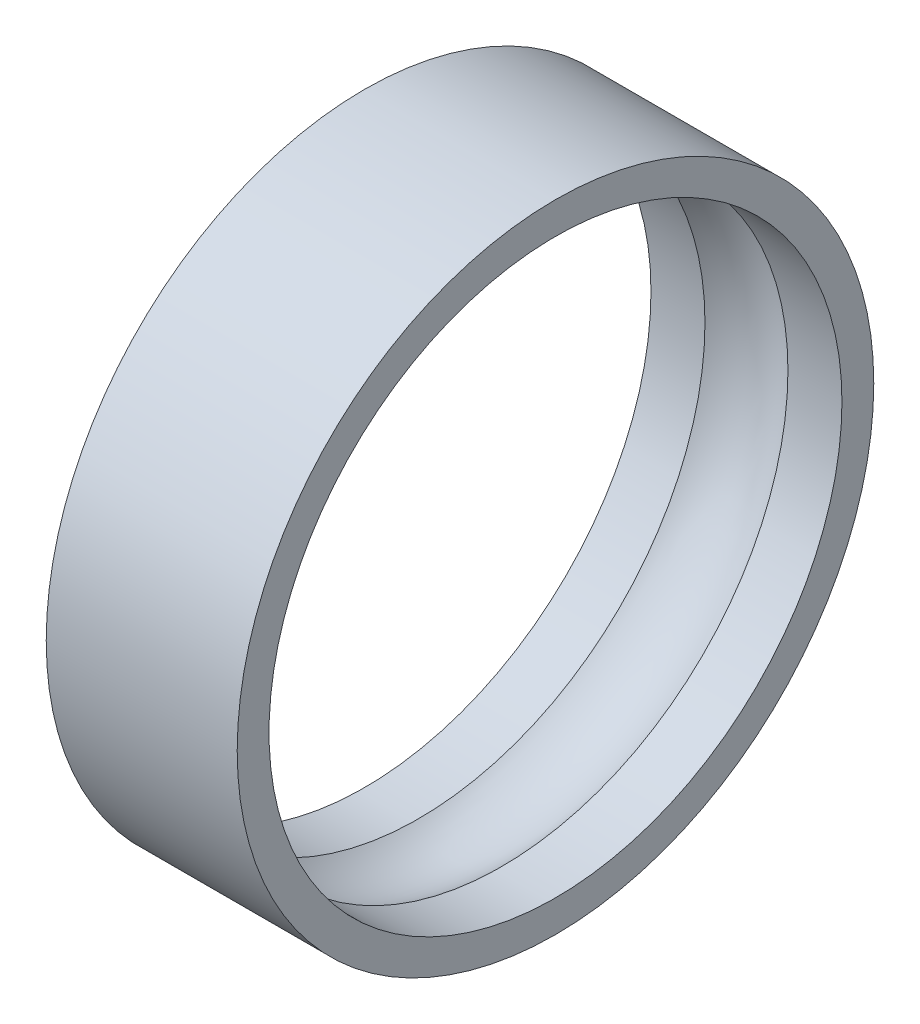
SolidWorks part; units mm, degrees
ref_plane "前视基准面" through (0, 0, 0) normal (0, 0, 1) x (1, 0, 0)
ref_plane "上视基准面" through (0, 0, 0) normal (0, 1, 0) x (1, 0, 0)
ref_plane "右视基准面" through (0, 0, 0) normal (1, 0, 0) x (0, 0, -1)
sketch "草图1" plane through (0, 0, 0) normal (0, 0, 1) x (1, 0, 0)
  line L0 (0, 4.848) -> (0, 0) construction
  line L1 (0, 7.8693) -> (0, 0) construction
  line L4 (-6, 5.75) -> (6, 5.75)
  line L6 (2.607, 3.75) -> (6, 3.75)
  line L7 (0, 5.75) -> (0, -14.25) construction
  line L8 (-6, 3.75) -> (-2.607, 3.75)
  line L10 (-6, 3.75) -> (-6, 5.75)
  line L11 (6, 3.75) -> (6, 5.75)
  line L12 (21.7151, -14.25) -> (-16.0886, -14.25) construction
  arc A0 (2.607, 3.75) -> (-2.607, 3.75) centre (0, 0.0821) ccw
  point P3 (0, 0)
  dimension "D3" = 20
  dimension "D1" = 12
  dimension "D2" = 5.75
  dimension "D4" = 2
revolve "旋转1" add sketch "草图1" angle 360 about L12
